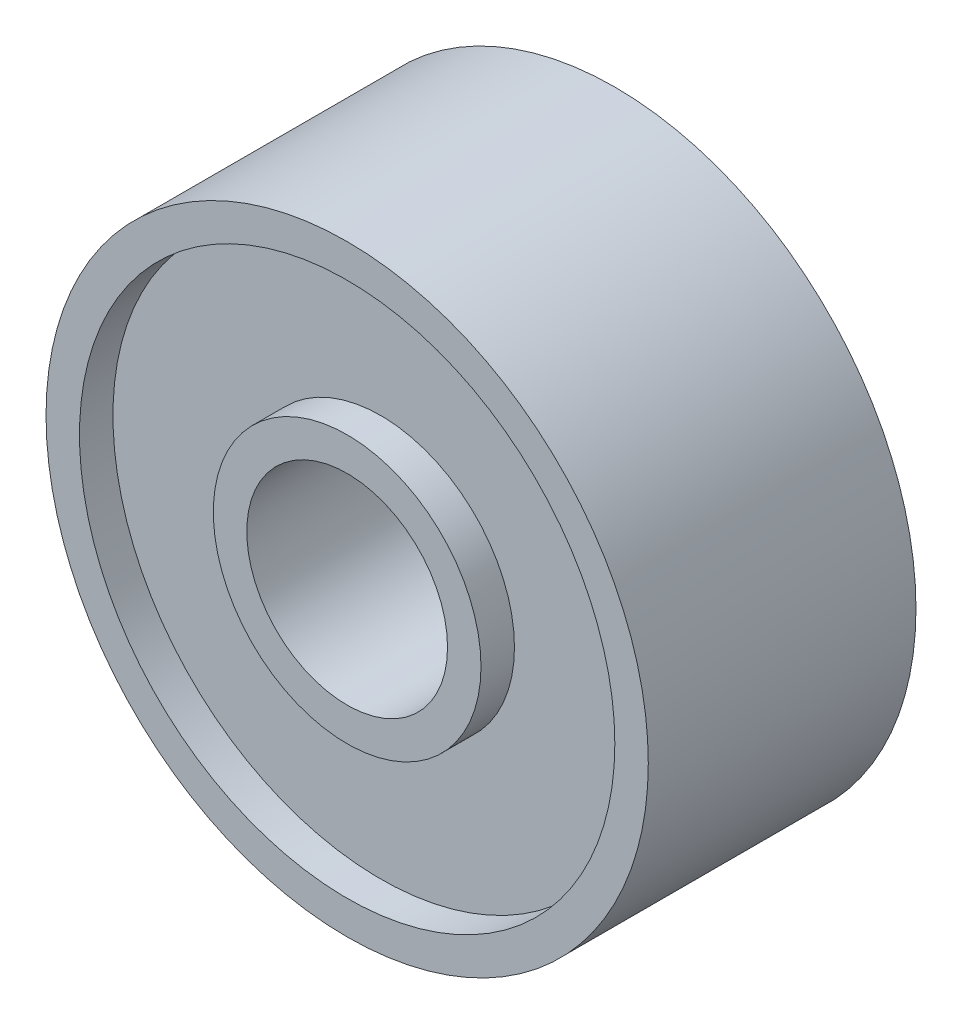
SolidWorks part; units mm, degrees
material "201 退火不鏽鋼 (SS)"
ref_plane "前基準面" through (0, 0, 0) normal (0, 0, 1) x (1, 0, 0)
ref_plane "上基準面" through (0, 0, 0) normal (0, 1, 0) x (1, 0, 0)
ref_plane "右基準面" through (0, 0, 0) normal (1, 0, 0) x (0, 0, -1)
sketch "草圖1" plane through (0, 0, 0) normal (0, 0, 1) x (1, 0, 0)
  circle A0 centre (0, 0) radius 4.5
  dimension "D1" = 9
extrude "填料-伸長1" add sketch "草圖1" along normal mid plane 4
sketch "草圖2" plane through (0, 0, 2) normal (0, 0, 1) x (1, 0, 0)
  circle A0 centre (0, 0) radius 1.5
  dimension "D1" = 3
extrude "除料-伸長1" cut sketch "草圖2" against normal through all
sketch "草圖3" plane through (0, 0, 2) normal (0, 0, 1) x (1, 0, 0)
  circle A0 centre (0, 0) radius 4
  circle A1 centre (0, 0) radius 2
  dimension "D1" = 8
  dimension "D2" = 4
extrude "除料-伸長2" cut sketch "草圖3" against normal blind 0.5
mirror "鏡射1" about plane through (0, 0, 0) normal (0, 0, 1) of "除料-伸長2"
